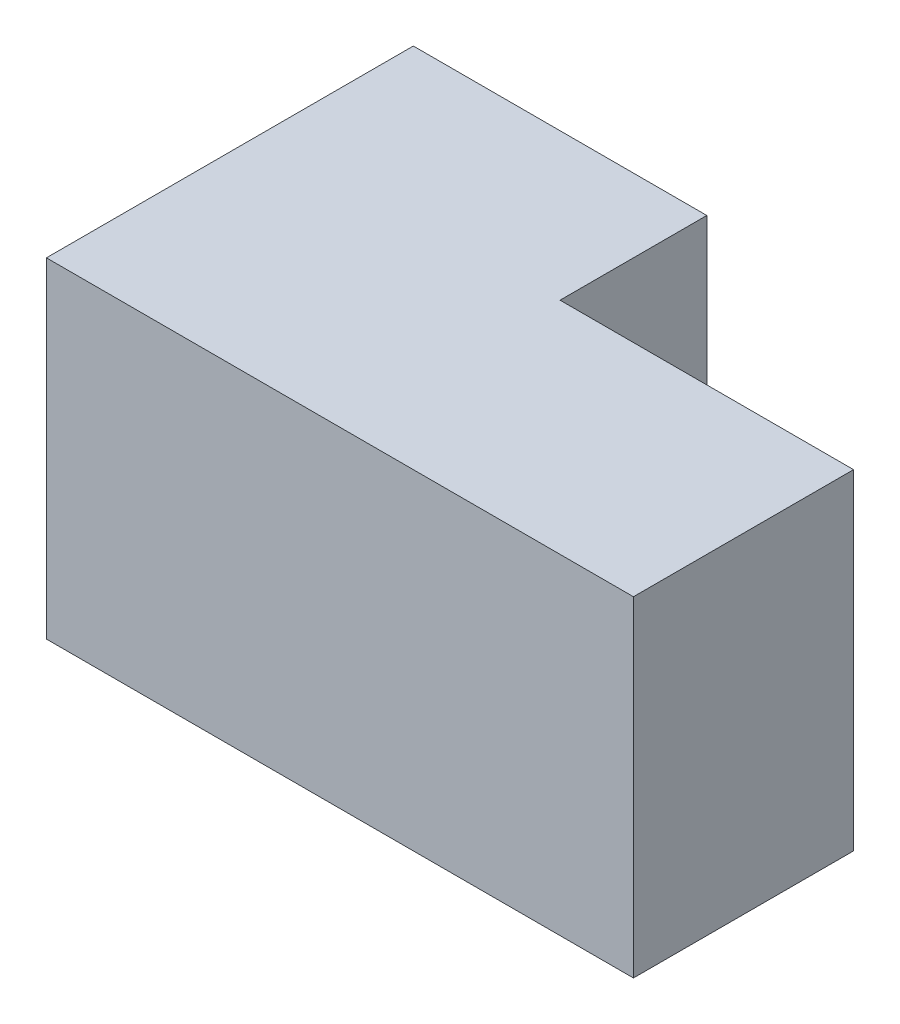
SolidWorks part; units mm, degrees
ref_plane "Front Plane" through (0, 0, 0) normal (0, 0, 1) x (1, 0, 0)
ref_plane "Top Plane" through (0, 0, 0) normal (0, 1, 0) x (1, 0, 0)
ref_plane "Right Plane" through (0, 0, 0) normal (1, 0, 0) x (0, 0, -1)
sketch "Sketch1" plane through (0, 0, 0) normal (0, 1, 0) x (1, 0, 0)
  line L0 (0, 31.75) -> (0, 0)
  line L1 (0, 0) -> (50.8, 0)
  line L2 (50.8, 0) -> (50.8, 19.05)
  line L3 (50.8, 19.05) -> (25.4, 19.05)
  line L4 (25.4, 19.05) -> (25.4, 31.75)
  line L5 (25.4, 31.75) -> (0, 31.75)
  dimension "D1" = 31.75
  dimension "D2" = 25.4
  dimension "D3" = 50.8
  dimension "D4" = 19.05
extrude "Boss-Extrude1" add sketch "Sketch1" along normal blind 28.575
